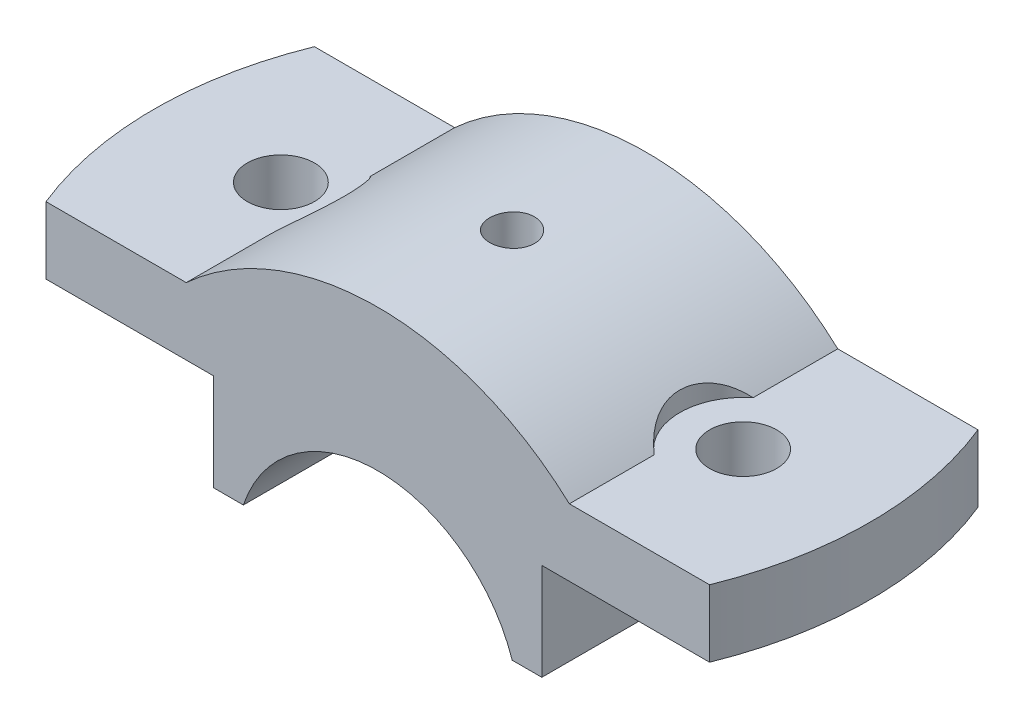
SolidWorks part; units mm, degrees
ref_plane "Front Plane" through (0, 0, 0) normal (0, 0, 1) x (1, 0, 0)
ref_plane "Top Plane" through (0, 0, 0) normal (0, 1, 0) x (1, 0, 0)
ref_plane "Right Plane" through (0, 0, 0) normal (1, 0, 0) x (0, 0, -1)
sketch "Sketch1" plane through (0, 0, 0) normal (0, 0, 1) x (1, 0, 0)
  line L0 (0, 0) -> (0, 41.7115) construction
  line L1 (18.0278, 6) -> (22, 6)
  line L2 (22, 6) -> (22, 19)
  line L3 (22, 19) -> (50, 19)
  line L4 (50, 19) -> (50, 28)
  line L5 (50, 28) -> (25.6905, 28)
  line L6 (-50, 28) -> (-25.6905, 28)
  line L7 (-50, 19) -> (-50, 28)
  line L8 (-22, 19) -> (-50, 19)
  line L9 (-22, 6) -> (-22, 19)
  line L10 (-18.0278, 6) -> (-22, 6)
  arc A0 (-18.0278, 6) -> (18.0278, 6) centre (0, 0) cw
  arc A1 (25.6905, 28) -> (-25.6905, 28) centre (0, 0) ccw
  dimension "D1" = 19
  dimension "D2" = 9
  dimension "D6" = 38
  dimension "D3" = 44
  dimension "D4" = 6
  dimension "D5" = 13
  dimension "D7" = 100
extrude "Boss-Extrude1" add sketch "Sketch1" along normal mid plane 36
hole_wizard "Ø6.0mm Dowel Hole1" positions "Sketch3" profile "Sketch2" hole size "Ø6.0" standard "ANSI Metric" end condition through all
sketch "Sketch3" plane through (0, 28, 0) normal (0, 1, 0) x (1, 0, 0)
  point P0 (-31, 0)
  dimension "D1" = 31
sketch "Sketch2" plane through (-31, 28, 0) normal (1, 0, 0) x (0, 0, 1)
  line L0 (0, 0) -> (0, 22)
  line L1 (0, 22) -> (4.5, 22)
  line L2 (4.5, 22) -> (4.5, 0)
  line L5 (4.5, 0) -> (0, 0)
  line L11 (0, -6.35) -> (0, 107.95) construction
  dimension "Thru Hole Dia." = 9
  dimension "Thru Hole Depth" = 22
mirror "Mirror1" about plane through (0, 0, 0) normal (1, 0, 0) of "Ø6.0mm Dowel Hole1"
sketch "Sketch6" plane through (0, 28, 0) normal (0, 1, 0) x (1, 0, 0)
  line L1 (-25.6905, -18) -> (-25.6905, 18) construction
  line L2 (-25.6905, -6.6377) -> (-25.6905, 6.6377)
  arc A0 (-25.6905, -6.6377) -> (-25.6905, 6.6377) centre (-31, 0) ccw
  dimension "D1" = 8.5
extrude "Cut-Extrude2" cut sketch "Sketch6" along normal blind 10
mirror "Mirror3" about plane through (0, 0, 0) normal (1, 0, 0) of "Cut-Extrude2"
hole_wizard "Ø6.0mm Dowel Hole2" positions "3DSketch1" profile "Sketch8" hole size "Ø6.0" standard "ANSI Metric"
sketch3d "3DSketch1"
  point P0 (0, 0, 0)
  point P3 (0.0049, 38, 0)
  dimension "D1" = 38
sketch "Sketch8" plane through (0.0049, 38, 0) normal (0, 0, 1) x (-1, 0.0001, 0)
  line L0 (0, 0) -> (0, 16)
  line L1 (0, 16) -> (3, 13)
  line L2 (3, 13) -> (3, 0)
  line L5 (3, 0) -> (0, 0)
  line L10 (0, 16) -> (-3, 13) construction
  line L11 (0, -6.35) -> (0, 107.95) construction
  dimension "Hole Dia." = 6
  dimension "Hole Depth" = 13
  dimension "Drill Angle" = 90
hole_wizard "Ø5.0mm Dowel Hole2" positions "3DSketch3" profile "Sketch11" hole size "Ø5.0" standard "ANSI Metric" end condition through all
sketch3d "3DSketch3"
  point P0 (0, 19, 0)
  dimension "D1" = 19
sketch "Sketch11" plane through (0, 19, 0) normal (0, 0, 1) x (1, 0, 0)
  line L0 (0, 0) -> (0, 19)
  line L1 (0, 19) -> (2.5, 19)
  line L2 (2.5, 19) -> (2.5, 0)
  line L5 (2.5, 0) -> (0, 0)
  line L11 (0, -6.35) -> (0, 107.95) construction
  dimension "Thru Hole Dia." = 5
  dimension "Thru Hole Depth" = 19
sketch "Sketch12" plane through (0, 28, 0) normal (0, 1, 0) x (1, 0, 0)
  line L0 (-25.6905, -18) -> (-50, -18) construction
  line L1 (-25.6905, 18) -> (-50, 18) construction
  arc A0 (-44.4972, -18) -> (-44.4972, 18) centre (0, 0) cw
  dimension "D1" = 48
extrude "Cut-Extrude3" cut sketch "Sketch12" against normal through all and the other way through all
mirror "Mirror4" about plane through (0, 0, 0) normal (1, 0, 0) of "Cut-Extrude3"
